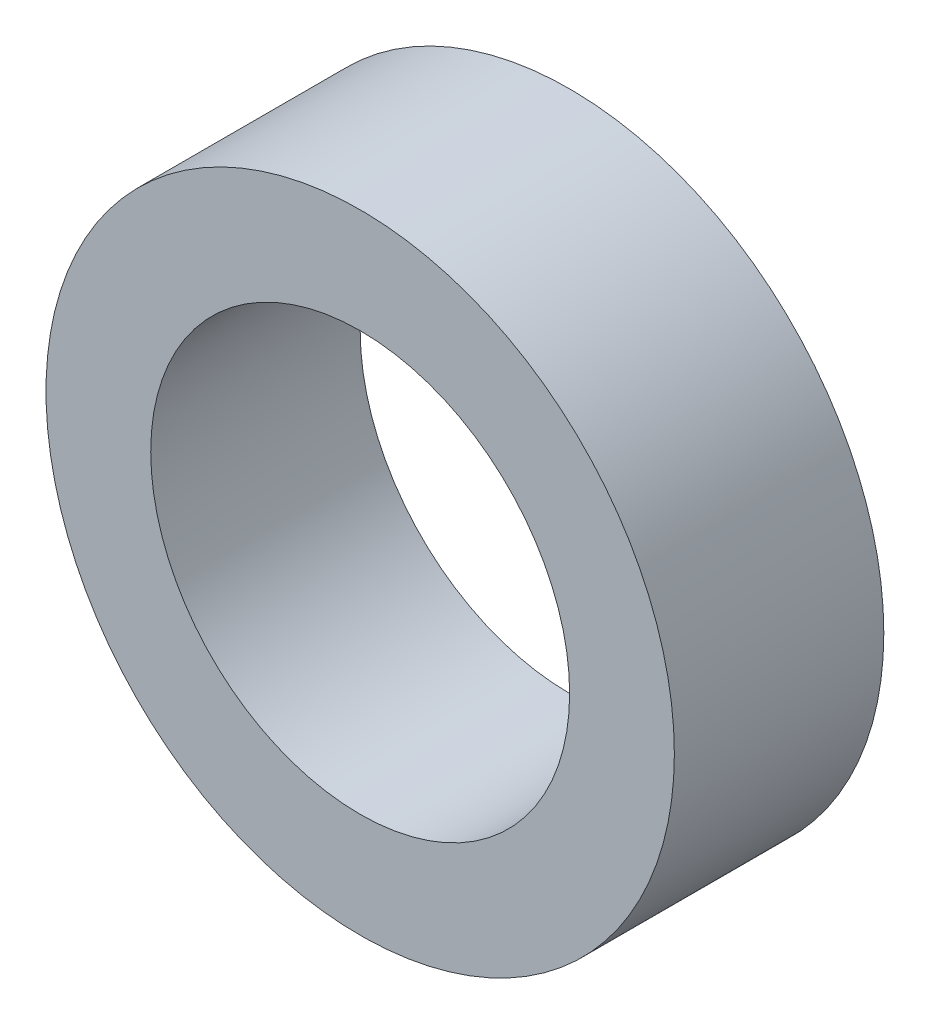
SolidWorks part; units mm, degrees
material "Aluminum Bronze"
ref_plane "Plan de face" through (0, 0, 0) normal (0, 0, 1) x (1, 0, 0)
ref_plane "Plan de dessus" through (0, 0, 0) normal (0, 1, 0) x (1, 0, 0)
ref_plane "Plan de droite" through (0, 0, 0) normal (1, 0, 0) x (0, 0, -1)
sketch "Sketch1" plane through (0, 0, 0) normal (0, 0, 1) x (1, 0, 0)
  circle A0 centre (0, 0) radius 4
  circle A1 centre (0, 0) radius 6
  dimension "D1" = 8
  dimension "D2" = 12
extrude "Boss-Extrude1" add sketch "Sketch1" along normal blind 4
